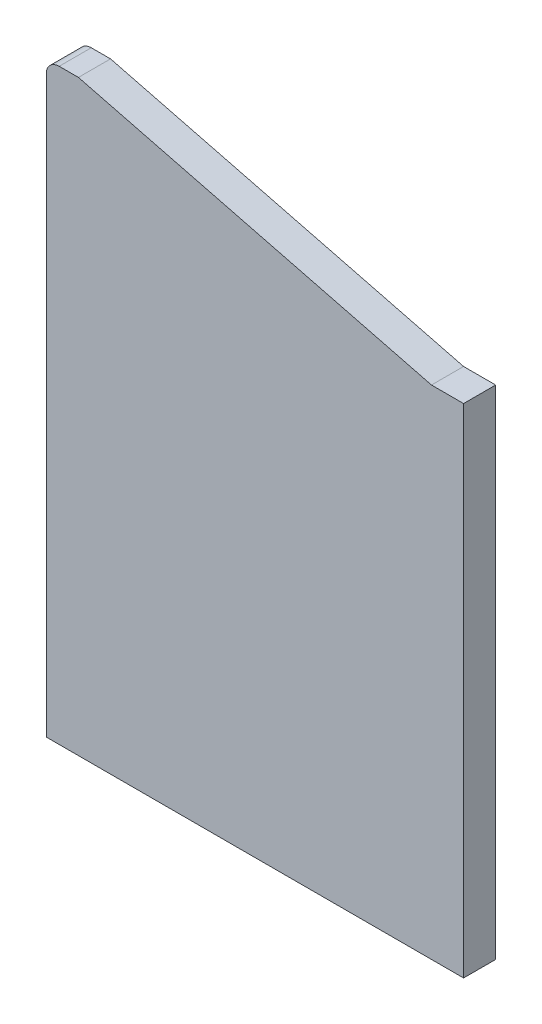
SolidWorks part; units mm, degrees
ref_plane "Plan de face" through (0, 0, 0) normal (0, 0, 1) x (1, 0, 0)
ref_plane "Plan de dessus" through (0, 0, 0) normal (0, 1, 0) x (1, 0, 0)
ref_plane "Plan de droite" through (0, 0, 0) normal (1, 0, 0) x (0, 0, -1)
sketch "Esquisse1" plane through (0, 0, 0) normal (0, 0, 1) x (1, 0, 0)
  line L0 (0, 183) -> (10, 183)
  line L1 (10, 183) -> (120, 155)
  line L2 (120, 155) -> (130, 155)
  line L3 (130, 155) -> (130, 0)
  line L4 (130, 0) -> (0, 0)
  line L5 (0, 0) -> (0, 183)
extrude "Boss.-Extru.1" add sketch "Esquisse1" along normal blind 10
fillet "Congé1" radius 4 1 edges at (0, 183, 5)
